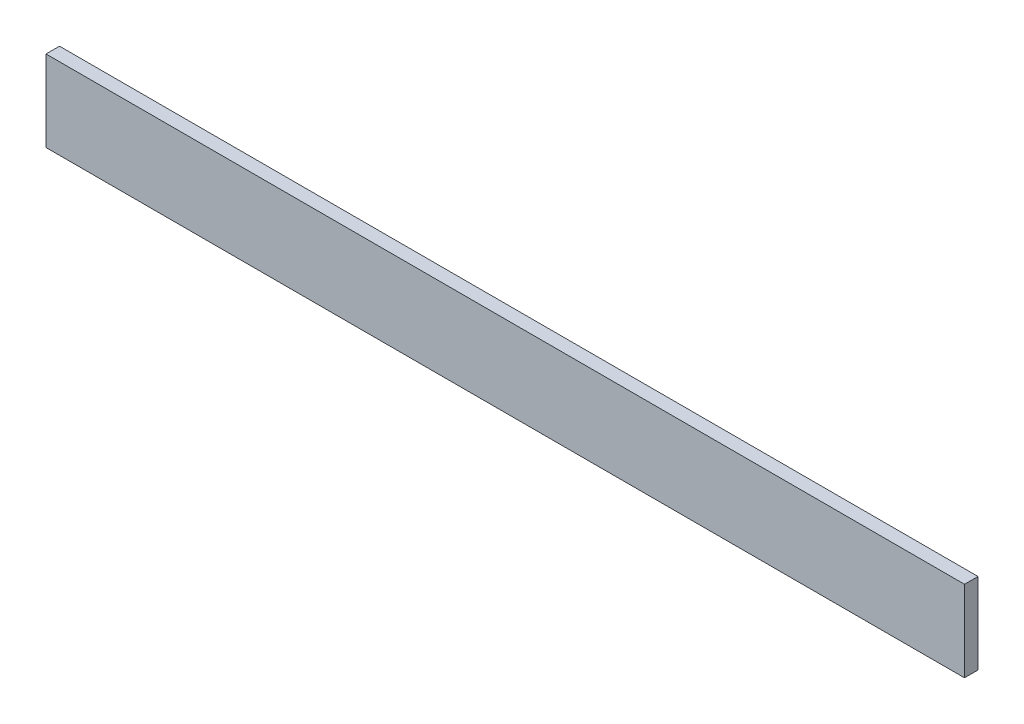
SolidWorks part; units mm, degrees
ref_plane "Front Plane" through (0, 0, 0) normal (0, 0, 1) x (1, 0, 0)
ref_plane "Top Plane" through (0, 0, 0) normal (0, 1, 0) x (1, 0, 0)
ref_plane "Right Plane" through (0, 0, 0) normal (1, 0, 0) x (0, 0, -1)
sketch "Sketch1" plane through (0, 0, 0) normal (0, 0, 1) x (1, 0, 0)
  line L1 (-101.8065, 43.5896) -> (114.0935, 43.5896)
  line L2 (-101.8065, 43.5896) -> (-101.8065, 24.5396)
  line L3 (-101.8065, 24.5396) -> (114.0935, 24.5396)
  line L4 (114.0935, 43.5896) -> (114.0935, 24.5396)
  dimension "D1" = 215.9
  dimension "D2" = 19.05
extrude "Boss-Extrude1" add sketch "Sketch1" along normal blind 3.175
